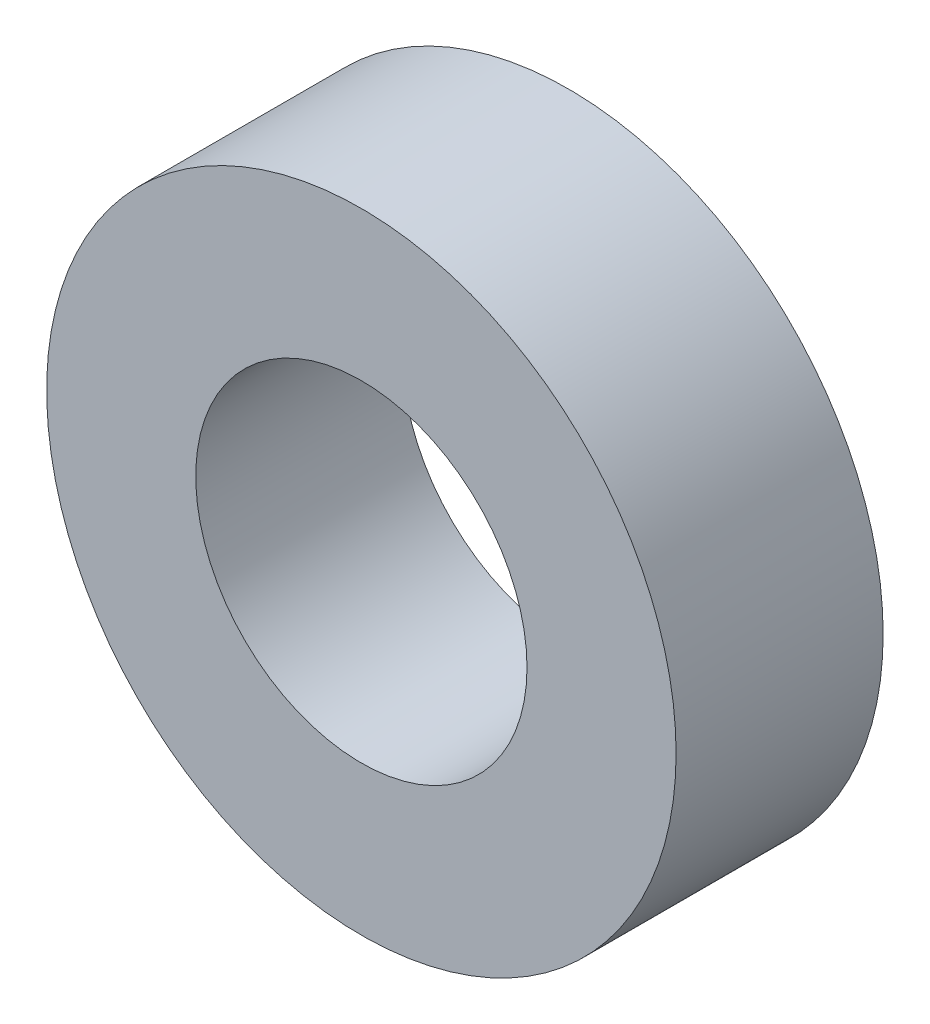
SolidWorks part; units mm, degrees
material "Nylon 6/10"
ref_plane "Front Plane" through (0, 0, 0) normal (0, 0, 1) x (1, 0, 0)
ref_plane "Top Plane" through (0, 0, 0) normal (0, 1, 0) x (1, 0, 0)
ref_plane "Right Plane" through (0, 0, 0) normal (1, 0, 0) x (0, 0, -1)
sketch "Sketch1" plane through (0, 0, 0) normal (0, 1, 0) x (1, 0, 0)
  line L0 (2.5, -1.5625) -> (4.75, -1.5625)
  line L1 (4.75, -1.5625) -> (4.75, 1.5625)
  line L2 (4.75, 1.5625) -> (2.5, 1.5625)
  line L3 (2.5, 1.5625) -> (2.5, -1.5625)
  line L4 (0, 1.5625) -> (0, -1.5625) construction
revolve "Revolve1" add sketch "Sketch1" angle 360 about L4
